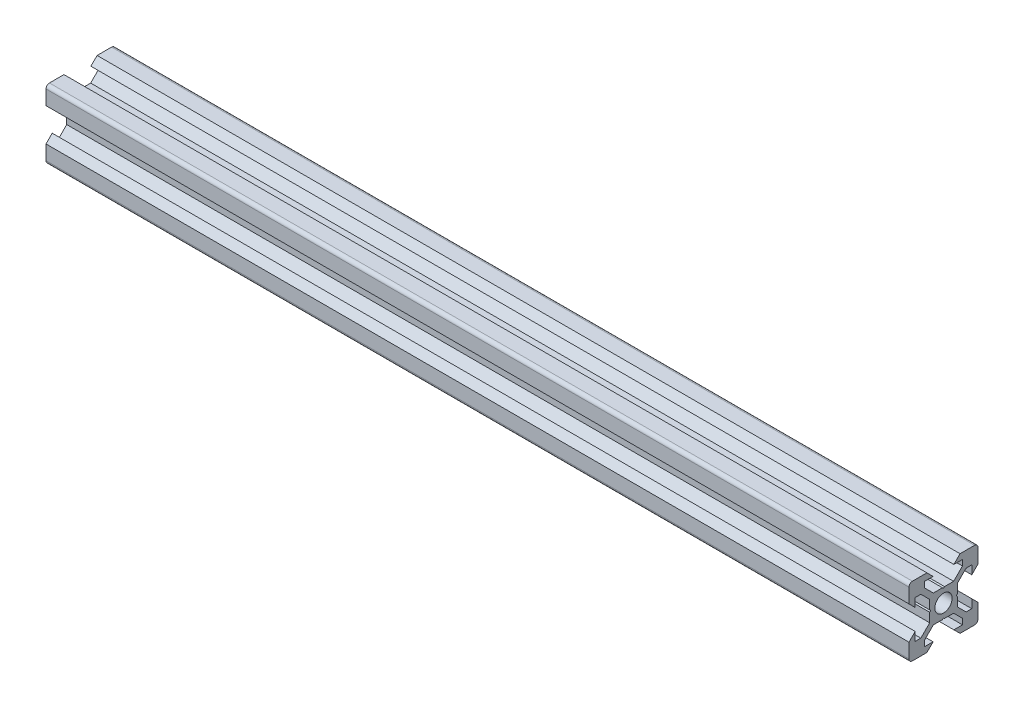
SolidWorks part; units mm, degrees
material "6063-T5"
material "6063-T5"
ref_plane "Plano frontal" through (0, 0, 0) normal (0, 0, 1) x (1, 0, 0)
ref_plane "Plano superior" through (0, 0, 0) normal (0, 1, 0) x (1, 0, 0)
ref_plane "Plano direito" through (0, 0, 0) normal (1, 0, 0) x (0, 0, -1)
sketch "Esboço1" plane through (0, 0, 0) normal (0, 0, 1) x (1, 0, 0)
  line L0 (0, 0) -> (250, 0)
  dimension "D1" = 250
other "Quadrado PF20-11 - PERFIL 2020 V-SLOT(1)"
ref_plane "Plano1" through (0, 0, 0) normal (1, 0, 0) x (0, 1, 0)
sketch "Sketch11" plane through (0, 0, 0) normal (1, 0, 0) x (0, 1, 0)
  line L0 (-4.8, 10) -> (-3, 8.2)
  line L1 (-3, 8.2) -> (-5.5, 8.2)
  line L2 (-5.5, 8.2) -> (-5.5, 6.5607)
  line L3 (-5.5, 6.5607) -> (-2.9393, 4)
  line L4 (-2.9393, 4) -> (-0.3, 4)
  line L5 (5.5, 6.5607) -> (2.9393, 4)
  line L6 (5.5, 8.2) -> (5.5, 6.5607)
  line L7 (3, 8.2) -> (5.5, 8.2)
  line L8 (4.8, 10) -> (3, 8.2)
  line L9 (-0.3, 4) -> (0, 3.7)
  line L10 (0.3, 4) -> (0, 3.7)
  line L11 (0.3, 4) -> (2.9393, 4)
  line L12 (9, 10) -> (4.8, 10)
  line L13 (10, 4.8) -> (8.2, 3)
  line L14 (10, 4.8) -> (10, 9)
  line L15 (8.2, 3) -> (8.2, 5.5)
  line L16 (8.2, 5.5) -> (6.5607, 5.5)
  line L17 (6.5607, 5.5) -> (4, 2.9393)
  line L18 (4.8, -10) -> (3, -8.2)
  line L19 (3, -8.2) -> (5.5, -8.2)
  line L20 (5.5, -8.2) -> (5.5, -6.5607)
  line L21 (5.5, -6.5607) -> (2.9393, -4)
  line L22 (2.9393, -4) -> (0.3, -4)
  line L23 (0.3, -4) -> (0, -3.7)
  line L24 (-0.3, -4) -> (0, -3.7)
  line L25 (-0.3, -4) -> (-2.9393, -4)
  line L26 (-5.5, -6.5607) -> (-2.9393, -4)
  line L27 (-5.5, -8.2) -> (-5.5, -6.5607)
  line L28 (-3, -8.2) -> (-5.5, -8.2)
  line L29 (-4.8, -10) -> (-3, -8.2)
  line L30 (-10, -4.8) -> (-10, -9)
  line L31 (-10, -4.8) -> (-8.2, -3)
  line L32 (-8.2, -3) -> (-8.2, -5.5)
  line L33 (-8.2, -5.5) -> (-6.5607, -5.5)
  line L34 (-6.5607, -5.5) -> (-4, -2.9393)
  line L35 (-4, -2.9393) -> (-4, -0.3)
  line L36 (-4, -0.3) -> (-3.7, 0)
  line L37 (-4, 0.3) -> (-3.7, 0)
  line L38 (-4, 0.3) -> (-4, 2.9393)
  line L39 (-6.5607, 5.5) -> (-4, 2.9393)
  line L40 (-8.2, 5.5) -> (-6.5607, 5.5)
  line L41 (-8.2, 3) -> (-8.2, 5.5)
  line L42 (-10, 4.8) -> (-8.2, 3)
  line L43 (-4.8, 10) -> (-9, 10)
  line L44 (4, 2.9393) -> (4, 0.3)
  line L45 (4, 0.3) -> (3.7, 0)
  line L46 (4, -0.3) -> (3.7, 0)
  line L47 (4, -0.3) -> (4, -2.9393)
  line L48 (6.5607, -5.5) -> (4, -2.9393)
  line L49 (8.2, -5.5) -> (6.5607, -5.5)
  line L50 (8.2, -3) -> (8.2, -5.5)
  line L51 (10, -4.8) -> (8.2, -3)
  line L52 (10, -9) -> (10, -4.8)
  line L53 (4.8, -10) -> (9, -10)
  line L106 (-10, 9) -> (-10, 4.8)
  line L107 (-9, -10) -> (-4.8, -10)
  arc A0 (10, 9) -> (9, 10) centre (9, 9) ccw
  arc A1 (9, -10) -> (10, -9) centre (9, -9) ccw
  arc A3 (-10, -9) -> (-9, -10) centre (-9, -9) ccw
  arc A4 (-9, 10) -> (-10, 9) centre (-9, 9) ccw
  circle A7 centre (0, 0) radius 2.5
  point P1 (-10, 10)
  point P3 (10, 10)
  point P4 (10, -10)
  point P68 (0, 0)
  point P70 (10, 0)
  point P71 (0, 0)
  point P72 (0, 0)
  point P113 (0, -10)
  point P114 (-10, -10)
  point P115 (-10, 0)
  point P116 (0, 10)
  point P118 (0, 0)
